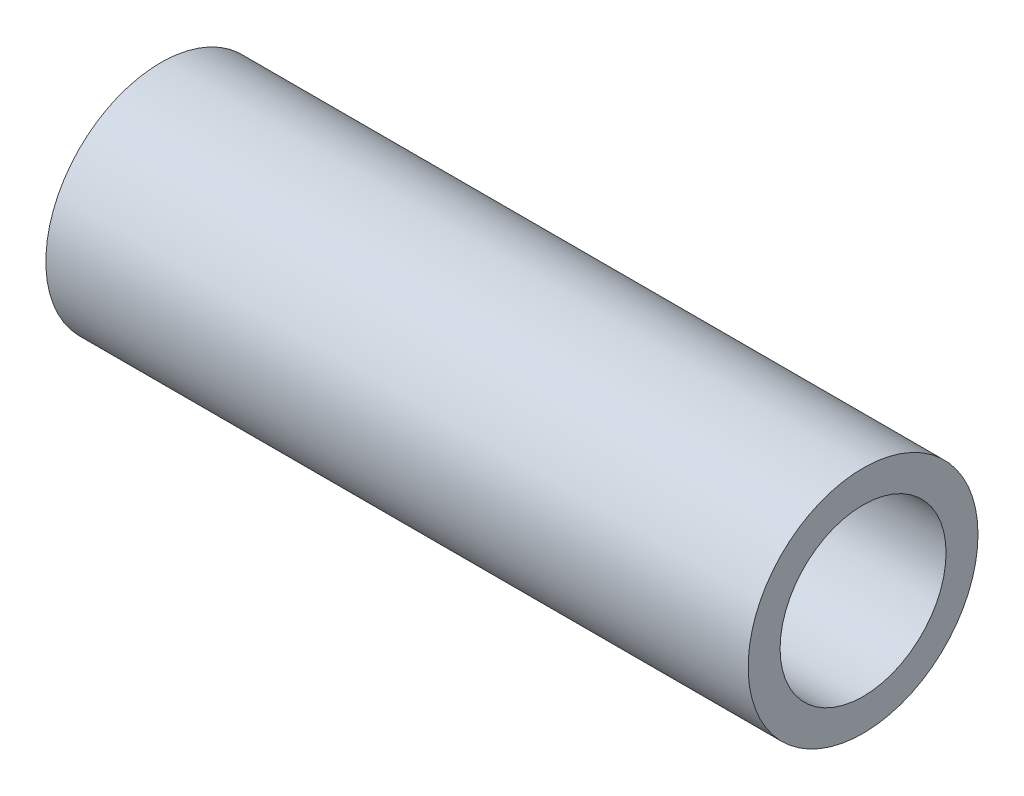
SolidWorks part; units mm, degrees
ref_plane "Front Plane" through (0, 0, 0) normal (0, 0, 1) x (1, 0, 0)
ref_plane "Top Plane" through (0, 0, 0) normal (0, 1, 0) x (1, 0, 0)
ref_plane "Right Plane" through (0, 0, 0) normal (1, 0, 0) x (0, 0, -1)
sketch "Sketch2" plane through (0, 0, 0) normal (1, 0, 0) x (0, 0, -1)
  circle A0 centre (0, 0) radius 9
  circle A1 centre (0, 0) radius 6.5
  dimension "D1" = 18
  dimension "D2" = 13
extrude "Boss-Extrude1" add sketch "Sketch2" along normal mid plane 55
